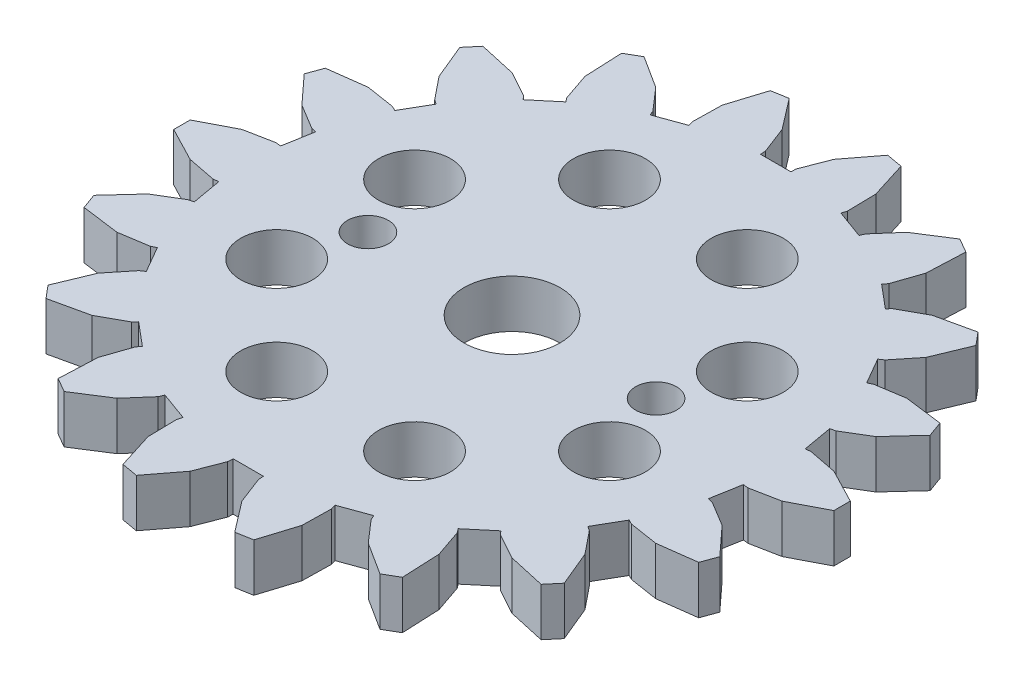
SolidWorks part; units mm, degrees
material "Acrylic (Medium-high impact)"
ref_plane "Front Plane" through (0, 0, 0) normal (0, 0, 1) x (1, 0, 0)
ref_plane "Top Plane" through (0, 0, 0) normal (0, 1, 0) x (1, 0, 0)
ref_plane "Right Plane" through (0, 0, 0) normal (1, 0, 0) x (0, 0, -1)
sketch "Sketch2" plane through (0, 0, 0) normal (0, 1, 0) x (1, 0, 0)
  line L0 (52.5387, 31.8425) -> (52.9668, 31.8929)
  line L1 (52.9668, 31.8929) -> (55.3456, 31.4261)
  line L2 (55.3456, 31.4261) -> (58.181, 29.9538)
  line L3 (58.181, 29.9538) -> (58.181, 28.5845)
  line L4 (58.181, 28.5845) -> (55.3456, 27.1121)
  line L5 (55.3456, 27.1121) -> (52.9668, 26.6454)
  line L6 (52.9668, 26.6454) -> (52.5387, 26.6957)
  line L7 (52.5387, 26.6957) -> (52.1012, 24.2147)
  line L8 (52.1012, 24.2147) -> (52.5208, 24.1156)
  line L9 (52.5208, 24.1156) -> (54.5964, 22.8636)
  line L10 (54.5964, 22.8636) -> (56.7575, 20.51)
  line L11 (56.7575, 20.51) -> (56.289, 19.2232)
  line L12 (56.289, 19.2232) -> (53.1208, 18.8096)
  line L13 (53.1208, 18.8096) -> (50.726, 19.1845)
  line L14 (50.726, 19.1845) -> (50.3409, 19.3783)
  line L15 (50.3409, 19.3783) -> (49.0813, 17.1964)
  line L16 (49.0813, 17.1964) -> (49.4416, 16.9599)
  line L17 (49.4416, 16.9599) -> (50.9638, 15.0733)
  line L18 (50.9638, 15.0733) -> (52.1897, 12.1228)
  line L19 (52.1897, 12.1228) -> (51.3094, 11.0736)
  line L20 (51.3094, 11.0736) -> (48.1906, 11.7686)
  line L21 (48.1906, 11.7686) -> (46.0686, 12.9399)
  line L22 (46.0686, 12.9399) -> (45.7729, 13.2537)
  line L23 (45.7729, 13.2537) -> (43.8429, 11.6343)
  line L24 (43.8429, 11.6343) -> (44.1008, 11.2887)
  line L25 (44.1008, 11.2887) -> (44.8859, 8.9954)
  line L26 (44.8859, 8.9954) -> (45.0286, 5.8036)
  line L27 (45.0286, 5.8036) -> (43.8427, 5.1188)
  line L28 (43.8427, 5.1188) -> (41.1496, 6.8384)
  line L29 (41.1496, 6.8384) -> (39.5561, 8.665)
  line L30 (39.5561, 8.665) -> (39.3857, 9.0611)
  line L31 (39.3857, 9.0611) -> (37.0183, 8.1993)
  line L32 (37.0183, 8.1993) -> (37.1423, 7.7863)
  line L33 (37.1423, 7.7863) -> (37.0956, 5.3628)
  line L34 (37.0956, 5.3628) -> (36.1382, 2.3147)
  line L35 (36.1382, 2.3147) -> (34.7894, 2.0769)
  line L36 (34.7894, 2.0769) -> (32.8471, 4.6136)
  line L37 (32.8471, 4.6136) -> (31.9745, 6.8751)
  line L38 (31.9745, 6.8751) -> (31.9497, 7.3056)
  line L39 (31.9497, 7.3056) -> (29.4305, 7.3056)
  line L40 (29.4305, 7.3056) -> (29.4056, 6.8751)
  line L41 (29.4056, 6.8751) -> (28.5331, 4.6136)
  line L42 (28.5331, 4.6136) -> (26.5908, 2.0769)
  line L43 (26.5908, 2.0769) -> (25.242, 2.3147)
  line L44 (25.242, 2.3147) -> (24.2845, 5.3628)
  line L45 (24.2845, 5.3628) -> (24.2379, 7.7863)
  line L46 (24.2379, 7.7863) -> (24.3618, 8.1993)
  line L47 (24.3618, 8.1993) -> (21.9945, 9.0611)
  line L48 (21.9945, 9.0611) -> (21.8241, 8.665)
  line L49 (21.8241, 8.665) -> (20.2305, 6.8384)
  line L50 (20.2305, 6.8384) -> (17.5375, 5.1188)
  line L51 (17.5375, 5.1188) -> (16.3515, 5.8036)
  line L52 (16.3515, 5.8036) -> (16.4943, 8.9954)
  line L53 (16.4943, 8.9954) -> (17.2794, 11.2887)
  line L54 (17.2794, 11.2887) -> (17.5373, 11.6343)
  line L55 (17.5373, 11.6343) -> (15.6073, 13.2537)
  line L56 (15.6073, 13.2537) -> (15.3116, 12.9399)
  line L57 (15.3116, 12.9399) -> (13.1896, 11.7686)
  line L58 (13.1896, 11.7686) -> (10.0708, 11.0736)
  line L59 (10.0708, 11.0736) -> (9.1904, 12.1228)
  line L60 (9.1904, 12.1228) -> (10.4164, 15.0733)
  line L61 (10.4164, 15.0733) -> (11.9386, 16.9599)
  line L62 (11.9386, 16.9599) -> (12.2989, 17.1964)
  line L63 (12.2989, 17.1964) -> (11.0392, 19.3783)
  line L64 (11.0392, 19.3783) -> (10.6542, 19.1845)
  line L65 (10.6542, 19.1845) -> (8.2594, 18.8096)
  line L66 (8.2594, 18.8096) -> (5.0911, 19.2232)
  line L67 (5.0911, 19.2232) -> (4.6227, 20.51)
  line L68 (4.6227, 20.51) -> (6.7838, 22.8636)
  line L69 (6.7838, 22.8636) -> (8.8594, 24.1156)
  line L70 (8.8594, 24.1156) -> (9.279, 24.2147)
  line L71 (9.279, 24.2147) -> (8.8414, 26.6957)
  line L72 (8.8414, 26.6957) -> (8.4133, 26.6454)
  line L73 (8.4133, 26.6454) -> (6.0345, 27.1121)
  line L74 (6.0345, 27.1121) -> (3.1991, 28.5845)
  line L75 (3.1991, 28.5845) -> (3.1991, 29.9538)
  line L76 (3.1991, 29.9538) -> (6.0345, 31.4261)
  line L77 (6.0345, 31.4261) -> (8.4133, 31.8929)
  line L78 (8.4133, 31.8929) -> (8.8414, 31.8425)
  line L79 (8.8414, 31.8425) -> (9.279, 34.3235)
  line L80 (9.279, 34.3235) -> (8.8594, 34.4226)
  line L81 (8.8594, 34.4226) -> (6.7838, 35.6747)
  line L82 (6.7838, 35.6747) -> (4.6227, 38.0282)
  line L83 (4.6227, 38.0282) -> (5.0911, 39.3151)
  line L84 (5.0911, 39.3151) -> (8.2594, 39.7287)
  line L85 (8.2594, 39.7287) -> (10.6542, 39.3537)
  line L86 (10.6542, 39.3537) -> (11.0392, 39.16)
  line L87 (11.0392, 39.16) -> (12.2989, 41.3418)
  line L88 (12.2989, 41.3418) -> (11.9386, 41.5783)
  line L89 (11.9386, 41.5783) -> (10.4164, 43.4649)
  line L90 (10.4164, 43.4649) -> (9.1904, 46.4154)
  line L91 (9.1904, 46.4154) -> (10.0708, 47.4647)
  line L92 (10.0708, 47.4647) -> (13.1896, 46.7696)
  line L93 (13.1896, 46.7696) -> (15.3116, 45.5984)
  line L94 (15.3116, 45.5984) -> (15.6073, 45.2846)
  line L95 (15.6073, 45.2846) -> (17.5373, 46.904)
  line L96 (17.5373, 46.904) -> (17.2794, 47.2496)
  line L97 (17.2794, 47.2496) -> (16.4943, 49.5428)
  line L98 (16.4943, 49.5428) -> (16.3515, 52.7346)
  line L99 (16.3515, 52.7346) -> (17.5375, 53.4195)
  line L100 (17.5375, 53.4195) -> (20.2305, 51.6998)
  line L101 (20.2305, 51.6998) -> (21.8241, 49.8733)
  line L102 (21.8241, 49.8733) -> (21.9945, 49.4772)
  line L103 (21.9945, 49.4772) -> (24.3618, 50.339)
  line L104 (24.3618, 50.339) -> (24.2379, 50.7519)
  line L105 (24.2379, 50.7519) -> (24.2845, 53.1754)
  line L106 (24.2845, 53.1754) -> (25.242, 56.2236)
  line L107 (25.242, 56.2236) -> (26.5908, 56.4614)
  line L108 (26.5908, 56.4614) -> (28.5331, 53.9247)
  line L109 (28.5331, 53.9247) -> (29.4056, 51.6631)
  line L110 (29.4056, 51.6631) -> (29.4305, 51.2327)
  line L111 (29.4305, 51.2327) -> (31.9497, 51.2327)
  line L112 (31.9497, 51.2327) -> (31.9745, 51.6631)
  line L113 (31.9745, 51.6631) -> (32.8471, 53.9247)
  line L114 (32.8471, 53.9247) -> (34.7894, 56.4614)
  line L115 (34.7894, 56.4614) -> (36.1382, 56.2236)
  line L116 (36.1382, 56.2236) -> (37.0956, 53.1754)
  line L117 (37.0956, 53.1754) -> (37.1423, 50.7519)
  line L118 (37.1423, 50.7519) -> (37.0183, 50.339)
  line L119 (37.0183, 50.339) -> (39.3857, 49.4772)
  line L120 (39.3857, 49.4772) -> (39.5561, 49.8733)
  line L121 (39.5561, 49.8733) -> (41.1496, 51.6998)
  line L122 (41.1496, 51.6998) -> (43.8427, 53.4195)
  line L123 (43.8427, 53.4195) -> (45.0286, 52.7346)
  line L124 (45.0286, 52.7346) -> (44.8859, 49.5428)
  line L125 (44.8859, 49.5428) -> (44.1008, 47.2496)
  line L126 (44.1008, 47.2496) -> (43.8429, 46.904)
  line L127 (43.8429, 46.904) -> (45.7729, 45.2846)
  line L128 (45.7729, 45.2846) -> (46.0686, 45.5984)
  line L129 (46.0686, 45.5984) -> (48.1906, 46.7696)
  line L130 (48.1906, 46.7696) -> (51.3094, 47.4647)
  line L131 (51.3094, 47.4647) -> (52.1897, 46.4154)
  line L132 (52.1897, 46.4154) -> (50.9638, 43.4649)
  line L133 (50.9638, 43.4649) -> (49.4416, 41.5783)
  line L134 (49.4416, 41.5783) -> (49.0813, 41.3418)
  line L135 (49.0813, 41.3418) -> (50.3409, 39.16)
  line L136 (50.3409, 39.16) -> (50.726, 39.3537)
  line L137 (50.726, 39.3537) -> (53.1208, 39.7287)
  line L138 (53.1208, 39.7287) -> (56.289, 39.3151)
  line L139 (56.289, 39.3151) -> (56.7575, 38.0282)
  line L140 (56.7575, 38.0282) -> (54.5964, 35.6747)
  line L141 (54.5964, 35.6747) -> (52.5208, 34.4226)
  line L142 (52.5208, 34.4226) -> (52.1012, 34.3235)
  line L143 (52.1012, 34.3235) -> (52.5387, 31.8425)
  line L144 (30.6901, 51.2327) -> (30.6901, 7.3056) construction
  line L145 (58.181, 29.2691) -> (3.1991, 29.2691) construction
sketch "Sketch3" plane through (0, 0, 0) normal (0, 1, 0) x (1, 0, 0)
  line L0 (30.6901, 51.2327) -> (30.6901, 7.3056) construction
  line L1 (18.6901, 29.2691) -> (42.6901, 29.2691) construction
  line L2 (58.181, 29.2691) -> (3.1991, 29.2691) construction
  line L3 (30.6901, 32.1459) -> (30.6901, 5.7347) construction
  circle A0 centre (30.6901, 29.2691) radius 4
  circle A1 centre (18.6901, 29.2691) radius 1.7
  circle A2 centre (42.6901, 29.2691) radius 1.7
  point P11 (30.6901, 29.2691)
  dimension "D1" = 8
  dimension "D2" = 3.4
  dimension "D3" = 12
extrude "Boss-Extrude1" add sketch "Sketch2" along normal blind 4
extrude "Cut-Extrude1" cut sketch "Sketch3" along normal up to next
sketch "Sketch4" plane through (0, 0, 0) normal (0, 1, 0) x (1, 0, 0)
  line L0 (30.6901, 29.2691) -> (3.1991, 29.2691) construction
  line L1 (3.1991, 29.9538) -> (3.1991, 28.5845) construction
  line L2 (30.6901, 29.2691) -> (0.7129, 41.6861) construction
  circle A0 centre (16.8319, 35.0094) radius 3
  point P0 (30.6901, 29.2691)
  dimension "D3" = 6
  dimension "D1" = 22.5
  dimension "D2" = 15
extrude "Cut-Extrude2" cut sketch "Sketch4" along normal up to next (4 mm away)
pattern_circular "CirPattern1" count 8 over 360 about axis through (30.6901, 0, -29.2691) along (0, 1, 0) of "Cut-Extrude2"
